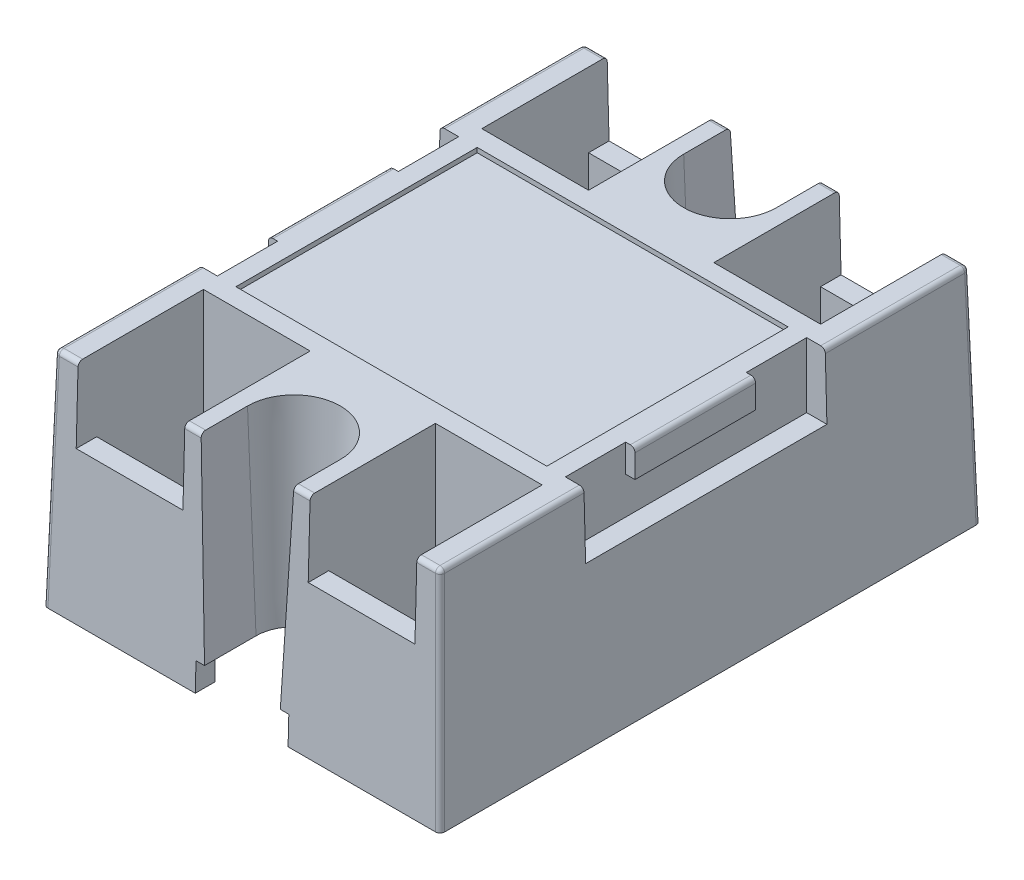
SolidWorks part; units mm, degrees
material "PBTP"
ref_plane "Front Plane" through (0, 0, 0) normal (0, 0, 1) x (1, 0, 0)
ref_plane "Top Plane" through (0, 0, 0) normal (0, 1, 0) x (1, 0, 0)
ref_plane "Right Plane" through (0, 0, 0) normal (1, 0, 0) x (0, 0, -1)
sketch "Sketch1" plane through (0, 0, 0) normal (0, 1, 0) x (1, 0, 0)
  line L1 (-20.75, 28.5) -> (20.75, 28.5)
  line L2 (-20.75, 28.5) -> (-20.75, -28.5)
  line L3 (-20.75, -28.5) -> (20.75, -28.5)
  line L4 (20.75, 28.5) -> (20.75, -28.5)
  line L5 (-20.75, 28.5) -> (20.75, -28.5) construction
  line L6 (-20.75, -28.5) -> (20.75, 28.5) construction
  point P0 (0, 0)
  dimension "D1" = 41.5
  dimension "D2" = 57
extrude "Boss-Extrude1" add sketch "Sketch1" along normal blind 24
sketch "Sketch2" plane through (0, 24, 0) normal (0, 1, 0) x (1, 0, 0)
  line L0 (0, 0) -> (0, -28.5) construction
  line L1 (-20.75, -28.5) -> (20.75, -28.5) construction
  line L3 (-5, -23.5) -> (5, -23.5) construction
  line L4 (-5, -23.5) -> (-5, -30.5)
  line L5 (-5, -30.5) -> (5, -30.5)
  line L6 (5, -23.5) -> (5, -30.5)
  line L7 (-5, -23.5) -> (5, -30.5) construction
  line L8 (-5, -30.5) -> (5, -23.5) construction
  arc A0 (-5, -23.5) -> (5, -23.5) centre (0, -23.5) cw
  point P5 (0, -27)
  dimension "D1" = 10
  dimension "D2" = 5
  dimension "D3" = 2
extrude "Cut-Extrude1" cut sketch "Sketch2" against normal offset from surface 3 draft 2.5
sketch "Sketch3" plane through (0, 24, 0) normal (0, 1, 0) x (1, 0, 0)
  line L0 (-20.75, -28.5) -> (-5, -28.5) construction
  line L1 (-18.25, -28.5) -> (-6.75, -28.5)
  line L2 (-18.25, -28.5) -> (-18.25, -15)
  line L3 (-18.25, -15) -> (-6.75, -15)
  line L4 (-6.75, -28.5) -> (-6.75, -15)
  line L5 (-18.25, -28.5) -> (-6.75, -15) construction
  line L6 (-18.25, -15) -> (-6.75, -28.5) construction
  line L7 (-20.75, 28.5) -> (-20.75, -28.5) construction
  line L10 (0, 0) -> (0, -28.5) construction
  line L11 (0, -28.5) -> (-5, -28.5) construction
  line L12 (18.25, -28.5) -> (6.75, -28.5)
  line L13 (18.25, -28.5) -> (18.25, -15)
  line L14 (6.75, -28.5) -> (6.75, -15)
  line L15 (18.25, -15) -> (6.75, -15)
  point P4 (-12.5, -21.75)
  dimension "D1" = 11.5
  dimension "D2" = 13.5
  dimension "D3" = 2.5
extrude "Cut-Extrude2" cut sketch "Sketch3" against normal blind 8
sketch "Sketch4" plane through (0, 16, 0) normal (0, 1, 0) x (1, 0, 0)
  line L0 (-6.75, -28.5) -> (-6.75, -15) construction
  line L1 (-18.25, -15) -> (-6.75, -15)
  line L2 (-18.25, -15) -> (-18.25, -26.5)
  line L3 (-18.25, -26.5) -> (-6.75, -26.5)
  line L4 (-6.75, -15) -> (-6.75, -26.5)
  line L5 (-18.25, -15) -> (-6.75, -26.5) construction
  line L6 (-18.25, -26.5) -> (-6.75, -15) construction
  line L7 (-18.25, -28.5) -> (-6.75, -28.5) construction
  line L8 (18.25, -28.5) -> (18.25, -15) construction
  line L9 (6.75, -15) -> (18.25, -15)
  line L10 (6.75, -15) -> (6.75, -26.5)
  line L11 (6.75, -26.5) -> (18.25, -26.5)
  line L12 (18.25, -15) -> (18.25, -26.5)
  line L13 (6.75, -15) -> (18.25, -26.5) construction
  line L14 (6.75, -26.5) -> (18.25, -15) construction
  point P4 (-12.5, -20.75)
  point P14 (12.5, -20.75)
  dimension "D1" = 2
extrude "Cut-Extrude3" cut sketch "Sketch4" against normal through all
mirror "Mirror1" about plane through (0, 0, 0) normal (0, 0, 1) of "Cut-Extrude3", "Cut-Extrude2", "Cut-Extrude1"
sketch "Sketch5" plane through (-20.75, 0, 0) normal (-1, 0, 0) x (0, 0, 1)
  line L0 (0, 0) -> (0, 24) construction
  line L1 (-28.5, 0) -> (28.5, 0) construction
  line L2 (-28.5, 24) -> (28.5, 24) construction
  line L4 (-13, 24) -> (13, 24)
  line L5 (-13, 24) -> (-13, 17)
  line L6 (-13, 17) -> (13, 17)
  line L7 (13, 24) -> (13, 17)
  line L8 (-13, 24) -> (13, 17) construction
  line L9 (-13, 17) -> (13, 24) construction
  point P10 (0, 20.5)
  dimension "D1" = 26
  dimension "D2" = 7
extrude "Cut-Extrude4" cut sketch "Sketch5" against normal blind 2
sketch "Sketch6" plane through (-18.75, 0, 0) normal (-1, 0, 0) x (0, 0, 1)
  line L0 (0, 17) -> (0, 24) construction
  line L1 (-13, 17) -> (13, 17) construction
  line L2 (13, 24) -> (-13, 24) construction
  line L4 (-6.5, 24) -> (6.5, 24)
  line L5 (-6.5, 24) -> (-6.5, 21)
  line L6 (-6.5, 21) -> (6.5, 21)
  line L7 (6.5, 24) -> (6.5, 21)
  line L8 (-6.5, 24) -> (6.5, 21) construction
  line L9 (-6.5, 21) -> (6.5, 24) construction
  point P10 (0, 22.5)
  dimension "D1" = 3
  dimension "D2" = 13
extrude "Boss-Extrude2" add sketch "Sketch6" along normal blind 1
mirror "Mirror2" about plane through (0, 0, 0) normal (1, 0, 0) of "Boss-Extrude2", "Cut-Extrude4"
sketch "Sketch7" plane through (0, 24, 0) normal (0, 1, 0) x (1, 0, 0)
  line L0 (-18.75, 13) -> (-18.75, -13) construction
  line L1 (-16.75, 13) -> (16.75, 13)
  line L2 (-16.75, 13) -> (-16.75, -13)
  line L3 (-16.75, -13) -> (16.75, -13)
  line L4 (16.75, 13) -> (16.75, -13)
  line L5 (-16.75, 13) -> (16.75, -13) construction
  line L6 (-16.75, -13) -> (16.75, 13) construction
  line L7 (18.25, -15) -> (6.75, -15) construction
  point P0 (0, 0)
  dimension "D1" = 2
  dimension "D2" = 2
extrude "Cut-Extrude5" cut sketch "Sketch7" against normal blind 0.5
sketch "Sketch8" plane through (0, 0, 0) normal (0, -1, 0) x (1, 0, 0)
  line L0 (-20.75, 28.5) -> (20.75, 28.5) construction
  line L1 (-19.25, 27) -> (19.25, 27)
  line L2 (-19.25, 27) -> (-19.25, -27)
  line L3 (-19.25, -27) -> (19.25, -27)
  line L4 (19.25, 27) -> (19.25, -27)
  line L5 (-19.25, 27) -> (19.25, -27) construction
  line L6 (-19.25, -27) -> (19.25, 27) construction
  line L7 (20.75, 28.5) -> (20.75, -28.5) construction
  point P0 (0, 0)
  dimension "D1" = 1.5
  dimension "D2" = 1.5
extrude "Cut-Extrude6" cut sketch "Sketch8" against normal blind 3
sketch "Sketch9" plane through (0, 0, -28.5) normal (0, 0, -1) x (-1, 0, 0)
  line L0 (-20.75, 0) -> (20.75, 0) construction
  line L1 (-5, 3) -> (5, 3)
  line L2 (-5, 3) -> (-5, 0)
  line L3 (-5, 0) -> (5, 0)
  line L4 (5, 3) -> (5, 0)
  line L5 (-5, 3) -> (5, 0) construction
  line L6 (-5, 0) -> (5, 3) construction
  line L7 (0, 1.5) -> (0, 0) construction
  line L8 (-4.0831, 3) -> (4.0831, 3) construction
  point P4 (0, 1.5)
  dimension "D1" = 10
extrude "Cut-Extrude7" cut sketch "Sketch9" against normal through all
draft "Draft1" type of draft neutral plane draft angle 1.5 faces to draft 6 face at (-11.0583, 13.4, -28.5) face at (11.0583, 13.4, -28.5) face at (-20.75, 16.25, 0) face at (-11.0583, 13.4, 28.5) face at (11.0583, 13.4, 28.5) face at (20.75, 16.25, 0) neutral plane through (0, 24, 0) neutral plane normal (0, 1, 0) parameters "D1"=1.5
fillet "Fillet1" radius 0.5 18 edges at (5.875, 24, -28.5) (-5.875, 24, -28.5) (5.875, 24, 28.5) (-5.875, 24, 28.5) (-19.5, 24, 28.5) (19.5, 24, 28.5) (19.5, 24, -28.5) (-19.5, 24, -28.5) (-21.0642, 12, -28.8142) (21.0642, 12, -28.8142) (21.0642, 12, 28.8142) (-21.0642, 12, 28.8142) (-20.75, 24, -20.75) (-19.75, 24, 0) (20.75, 24, -20.75) (19.75, 24, 0) (-20.75, 24, 20.75) (20.75, 24, 20.75)
sketch "Sketch10" plane through (0, 3, 0) normal (0, -1, 0) x (1, 0, 0)
  line L0 (19.25, 27) -> (5, 27) construction
  line L1 (19.25, -27) -> (19.25, 27) construction
  circle A0 centre (7, 7.25) radius 1.25
  dimension "D1" = 2.5
  dimension "D2" = 19.75
  dimension "D3" = 12.25
extrude "Boss-Extrude3" add sketch "Sketch10" along normal blind 2.5
chamfer "Chamfer1" distance 0.25 angle 45 1 edges at (7, 0.5, 6)
